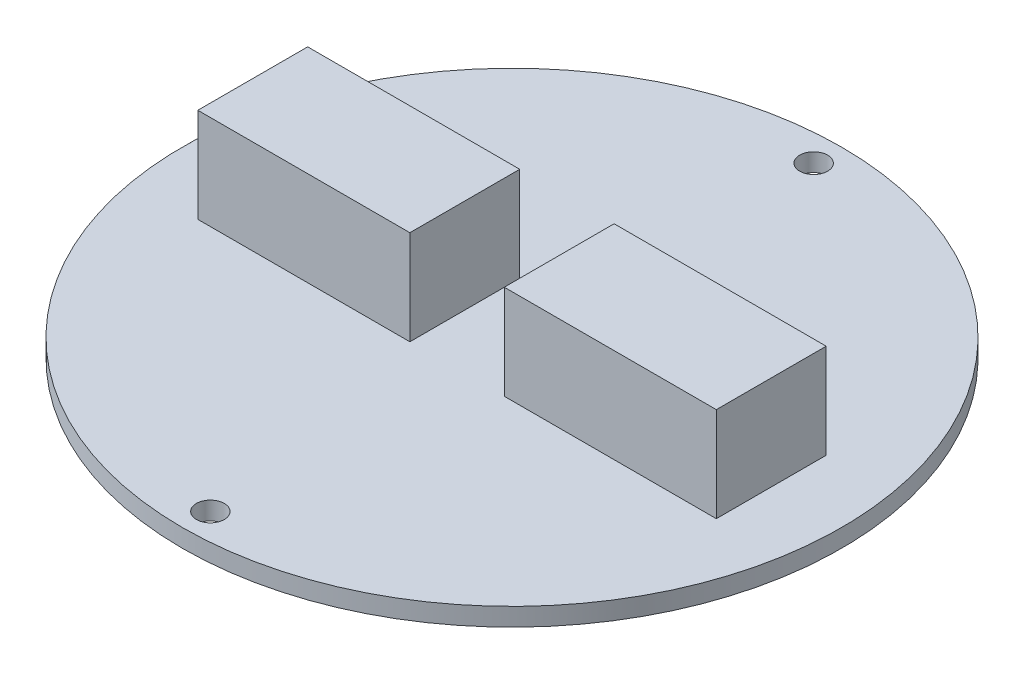
SolidWorks part; units mm, degrees
ref_plane "Front Plane" through (0, 0, 0) normal (0, 0, 1) x (1, 0, 0)
ref_plane "Top Plane" through (0, 0, 0) normal (0, 1, 0) x (1, 0, 0)
ref_plane "Right Plane" through (0, 0, 0) normal (1, 0, 0) x (0, 0, -1)
sketch "Sketch1" plane through (0, 0, 0) normal (0, 1, 0) x (1, 0, 0)
  circle A0 centre (0, 0) radius 30
  dimension "D1" = 60
extrude "Boss-Extrude1" add sketch "Sketch1" along normal blind 1.64
sketch "Sketch2" plane through (0, 1.64, 0) normal (0, 1, 0) x (1, 0, 0)
  line L0 (0, -27.46) -> (0, -30) construction
  line L1 (0, 27.46) -> (0, 30) construction
  circle A0 centre (0, 27.46) radius 1.27
  circle A1 centre (0, -27.46) radius 1.27
  circle A2 centre (0, 0) radius 30 construction
  dimension "D1" = 2.54
  dimension "D2" = 2.54
  dimension "D3" = 2.54
extrude "Cut-Extrude1" cut sketch "Sketch2" against normal through all
sketch "Sketch3" plane through (0, 1.64, 0) normal (0, 1, 0) x (1, 0, 0)
  line L0 (-23.6, 0) -> (-30, 0) construction
  line L1 (-23.6, -5) -> (-4.296, -5)
  line L2 (-23.6, -5) -> (-23.6, 5)
  line L3 (-23.6, 5) -> (-4.296, 5)
  line L4 (-4.296, -5) -> (-4.296, 5)
  line L5 (-23.6, -5) -> (-4.296, 5) construction
  line L6 (-23.6, 5) -> (-4.296, -5) construction
  line L7 (4.296, -5) -> (23.6, -5)
  line L8 (4.296, -5) -> (4.296, 5)
  line L9 (4.296, 5) -> (23.6, 5)
  line L10 (23.6, -5) -> (23.6, 5)
  line L11 (4.296, -5) -> (23.6, 5) construction
  line L12 (4.296, 5) -> (23.6, -5) construction
  line L13 (23.6, 0) -> (30, 0) construction
  circle A2 centre (0, 0) radius 30 construction
  point P0 (-13.948, 0)
  point P5 (13.948, 0)
  dimension "D1" = 19.304
  dimension "D2" = 19.304
  dimension "D3" = 10
  dimension "D4" = 10
  dimension "D5" = 6.4
extrude "Boss-Extrude2" add sketch "Sketch3" along normal blind 8.6
